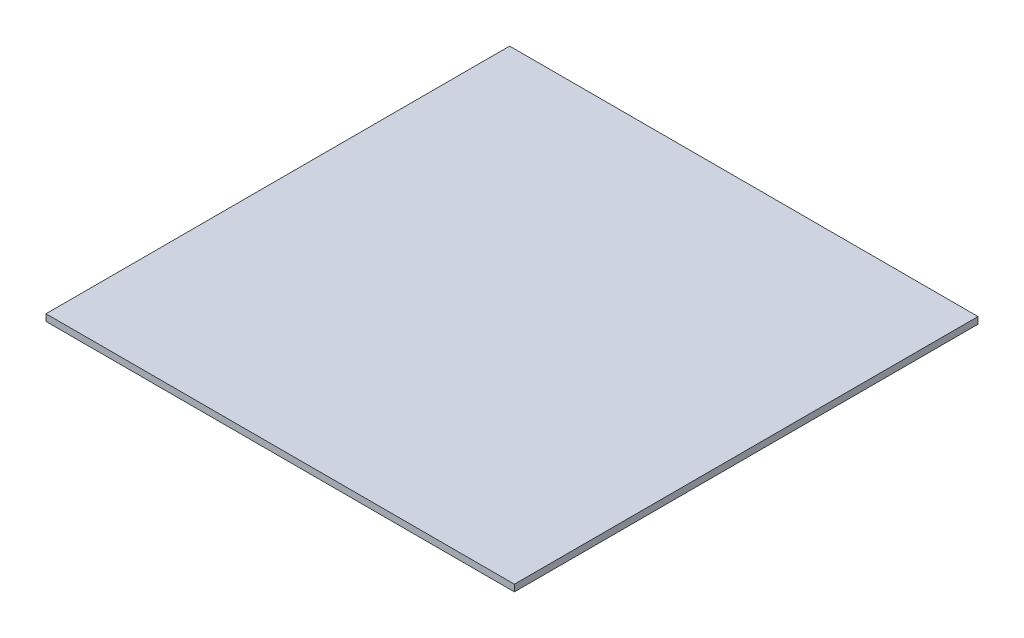
SolidWorks part; units mm, degrees
ref_plane "Front Plane" through (0, 0, 0) normal (0, 0, 1) x (1, 0, 0)
ref_plane "Top Plane" through (0, 0, 0) normal (0, 1, 0) x (1, 0, 0)
ref_plane "Right Plane" through (0, 0, 0) normal (1, 0, 0) x (0, 0, -1)
sketch "Sketch1" plane through (0, 0, 0) normal (0, 1, 0) x (1, 0, 0)
  line L0 (0, 0) -> (-100, -173.2051) construction
  line L1 (100, 173.2051) -> (-100, 173.2051)
  line L2 (-100, 173.2051) -> (-200, 0)
  line L3 (-200, 0) -> (-100, -173.2051)
  line L4 (-100, -173.2051) -> (100, -173.2051)
  line L5 (100, -173.2051) -> (200, 0)
  line L6 (200, 0) -> (100, 173.2051)
  line L7 (200, 0) -> (100, -173.2051)
  line L8 (100, -173.2051) -> (200, -346.4102)
  line L9 (200, -346.4102) -> (400, -346.4102)
  line L10 (400, -346.4102) -> (500, -173.2051)
  line L11 (500, -173.2051) -> (400, 0)
  line L12 (400, 0) -> (200, 0)
  line L13 (100, 173.2051) -> (200, 0)
  line L14 (200, 0) -> (400, 0)
  line L15 (400, 0) -> (500, 173.2051)
  line L16 (500, 173.2051) -> (400, 346.4102)
  line L17 (400, 346.4102) -> (200, 346.4102)
  line L18 (200, 346.4102) -> (100, 173.2051)
  line L19 (0, 0) -> (0, 173.2051) construction
  line L20 (300, 173.2051) -> (500, 173.2051) construction
  line L21 (-200, 0) -> (-200, 346.4102)
  line L22 (-200, 346.4102) -> (200, 346.4102)
  line L23 (400, 346.4102) -> (500, 346.4102)
  line L24 (500, 346.4102) -> (500, -346.4102)
  line L25 (500, -346.4102) -> (-200, -346.4102)
  line L26 (-200, -346.4102) -> (-200, 0)
  circle A0 centre (0, 0) radius 173.2051 construction
  circle A1 centre (300, -173.2051) radius 173.2051 construction
  circle A2 centre (300, 173.2051) radius 173.2051 construction
  dimension "D1" = 200
  dimension "200" = 200
  dimension "D2" = 692.8203
  dimension "D3" = 700
extrude "Boss-Extrude1" add sketch "Sketch1" along normal blind 10 contours L5 L6 L1 L2 L3 L4 | L17 L18 L6 L12 L15 L16 | L11 L12 L5 L8 L9 L10 | L22 L21 L2 L1 L18 | L26 L25 L8 L4 L3 | L24 L15 L11 | L24 L23 L16 | L25 L24 L10
sketch "Sketch2" plane through (0, 10, 0) normal (0, 1, 0) x (1, 0, 0)
  line L0 (500, -346.4102) -> (-200, -346.4102)
  line L1 (-200, -346.4102) -> (-200, 346.4102)
  dimension "D1" = 692.8203
  dimension "D2" = 700
